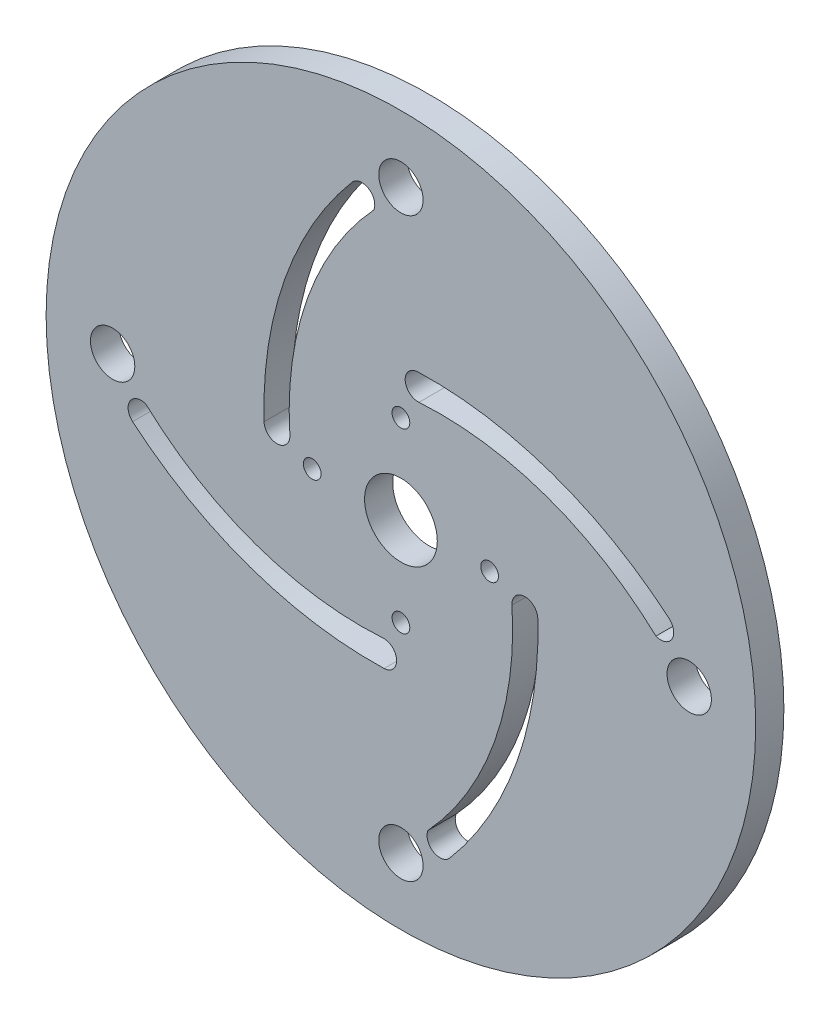
SolidWorks part; units mm, degrees
ref_plane "Front Plane" through (0, 0, 0) normal (0, 0, 1) x (1, 0, 0)
ref_plane "Top Plane" through (0, 0, 0) normal (0, 1, 0) x (1, 0, 0)
ref_plane "Right Plane" through (0, 0, 0) normal (1, 0, 0) x (0, 0, -1)
sketch "Sketch1" plane through (0, 0, 0) normal (0, 0, 1) x (1, 0, 0)
  circle A13 centre (0, 0) radius 40
  circle A14 centre (0, 0) radius 4.1
  circle A15 centre (10, 0) radius 1
  circle A16 centre (0, -10) radius 1
  circle A17 centre (-10, 0) radius 1
  circle A18 centre (0, 10) radius 1
  circle A19 centre (0, 32.5) radius 2.5
  circle A20 centre (32.5, 0) radius 2.5
  circle A21 centre (0, -32.5) radius 2.5
  circle A22 centre (-32.5, 0) radius 2.5
  arc A25 (1.8929, 15.4291) -> (30.2441, 5.5057) centre (3.1418, -26.4643) cw
  arc A26 (2.0331, 12.519) -> (28.7542, 3.0572) centre (4.4137, -23.2203) cw
  arc A27 (28.7542, 3.0572) -> (30.2441, 5.5057) centre (29.3059, 4.3991) ccw
  arc A28 (1.8929, 15.4291) -> (2.0331, 12.519) centre (1.9363, 13.9728) ccw
  arc A29 (15.4291, -1.8929) -> (5.5057, -30.2441) centre (-26.4643, -3.1418) cw
  arc A30 (3.0572, -28.7542) -> (5.5057, -30.2441) centre (4.3991, -29.3059) ccw
  arc A31 (12.519, -2.0331) -> (3.0572, -28.7542) centre (-23.2203, -4.4137) cw
  arc A32 (15.4291, -1.8929) -> (12.519, -2.0331) centre (13.9728, -1.9363) ccw
  arc A33 (-1.8929, -15.4291) -> (-30.2441, -5.5057) centre (-3.1418, 26.4643) cw
  arc A34 (-28.7542, -3.0572) -> (-30.2441, -5.5057) centre (-29.3059, -4.3991) ccw
  arc A35 (-2.0331, -12.519) -> (-28.7542, -3.0572) centre (-4.4137, 23.2203) cw
  arc A36 (-1.8929, -15.4291) -> (-2.0331, -12.519) centre (-1.9363, -13.9728) ccw
  arc A37 (-15.4291, 1.8929) -> (-5.5057, 30.2441) centre (26.4643, 3.1418) cw
  arc A38 (-3.0572, 28.7542) -> (-5.5057, 30.2441) centre (-4.3991, 29.3059) ccw
  arc A39 (-12.519, 2.0331) -> (-3.0572, 28.7542) centre (23.2203, 4.4137) cw
  arc A40 (-15.4291, 1.8929) -> (-12.519, 2.0331) centre (-13.9728, 1.9363) ccw
  point P7 (0, 0)
  point P15 (0, 0)
  point P16 (-5.2401, 29.3729)
  point P55 (-5.6678, 29.3729)
  point P56 (0, 0)
  point P57 (-3.4577, 27.6618)
  point P58 (0, 0)
  point P59 (0, 0)
  point P60 (0, 0)
  point P61 (0, 0)
  point P62 (-29.3059, -4.4137)
  dimension "D1" = 10
  dimension "D2" = 32.5
  dimension "D3" = 4
extrude "Boss-Extrude1" add sketch "Sketch1" along normal blind 3.175 contours A13
sketch "Sketch2" plane through (0, 0, 3.175) normal (0, 0, 1) x (1, 0, 0)
  arc A0 (-13.8528, 1.5788) -> (-4.3991, 29.3059) centre (23.2203, 4.4137) cw
  arc A1 (-3.0572, 28.7542) -> (-12.519, 2.0331) centre (23.2203, 4.4137) ccw construction
  point P6 (0, 0)
equation "\"D\"= 6in"
